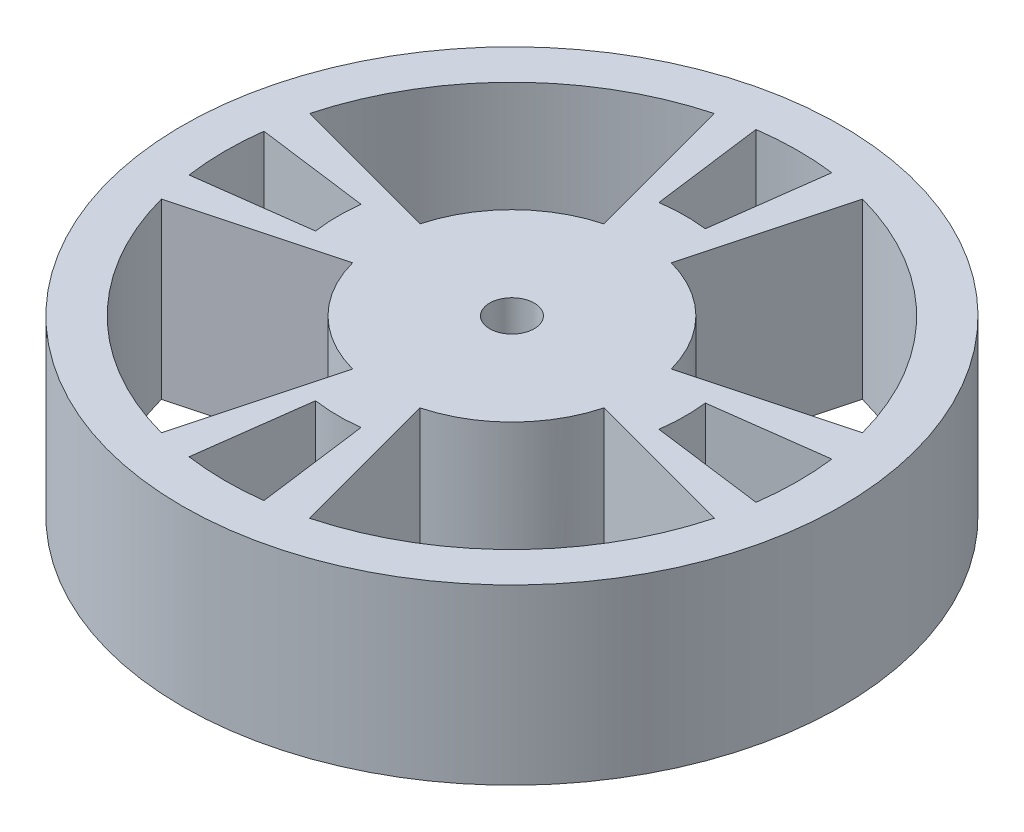
SolidWorks part; units mm, degrees
ref_plane "Front Plane" through (0, 0, 0) normal (0, 0, 1) x (1, 0, 0)
ref_plane "Top Plane" through (0, 0, 0) normal (0, 1, 0) x (1, 0, 0)
ref_plane "Right Plane" through (0, 0, 0) normal (1, 0, 0) x (0, 0, -1)
sketch "Sketch1" plane through (0, 0, 0) normal (0, 1, 0) x (1, 0, 0)
  circle A0 centre (0, 0) radius 9.525
  dimension "D1" = 19.05
extrude "Boss-Extrude1" add sketch "Sketch1" along normal blind 2.54
sketch "Sketch3" plane through (0, 2.54, 0) normal (0, 1, 0) x (1, 0, 0)
  line L0 (0, 0) -> (24.13, 0) construction
  line L1 (0, 0) -> (0, 24.13) construction
  line L2 (0, 0) -> (23.3078, 6.2453) construction
  line L3 (-2.4653, 9.2004) -> (-5.4236, 20.241)
  line L4 (9.2004, 2.4653) -> (20.241, 5.4236)
  line L5 (-9.2004, 2.4653) -> (-20.241, 5.4236)
  line L6 (0, 0) -> (17.0625, 17.0625) construction
  line L8 (2.4653, 9.2004) -> (5.4236, 20.241)
  line L9 (9.2004, -2.4653) -> (20.241, -5.4236)
  line L10 (2.4653, -9.2004) -> (5.4236, -20.241)
  line L11 (-9.2004, -2.4653) -> (-20.241, -5.4236)
  line L12 (-2.4653, -9.2004) -> (-5.4236, -20.241)
  circle A0 centre (0, 0) radius 24.13
  circle A2 centre (0, 0) radius 20.955 construction
  circle A3 centre (0, 0) radius 9.525 construction
  arc A4 (-9.2004, 2.4653) -> (-2.4653, 9.2004) centre (0, 0) cw
  arc A5 (9.2004, 2.4653) -> (2.4653, 9.2004) centre (0, 0) ccw
  arc A8 (20.241, 5.4236) -> (5.4236, 20.241) centre (0, 0) ccw
  arc A9 (-20.241, 5.4236) -> (-5.4236, 20.241) centre (0, 0) cw
  arc A10 (9.2004, -2.4653) -> (2.4653, -9.2004) centre (0, 0) cw
  arc A11 (20.241, -5.4236) -> (5.4236, -20.241) centre (0, 0) cw
  arc A12 (-20.241, -5.4236) -> (-5.4236, -20.241) centre (0, 0) ccw
  arc A13 (-9.2004, -2.4653) -> (-2.4653, -9.2004) centre (0, 0) ccw
  dimension "D1" = 48.26
  dimension "D2" = 15
  dimension "D4" = 3.175
  dimension "D3" = 45
extrude "Boss-Extrude2" add sketch "Sketch3" along normal blind 12.7
sketch "Sketch4" plane through (0, 15.24, 0) normal (0, 1, 0) x (1, 0, 0)
  line L0 (0, 0) -> (24.13, 0) construction
  line L1 (0, 0) -> (0, 24.13) construction
  line L2 (12.6046, 1.5541) -> (20.7891, 2.6316)
  line L5 (12.5705, -1.8088) -> (20.7553, -2.8863)
  line L6 (-12.6046, 1.5541) -> (-20.7891, 2.6316)
  line L7 (-12.5705, -1.8088) -> (-20.7553, -2.8863)
  line L8 (0, 0) -> (17.0625, 17.0625) construction
  line L9 (1.5541, 12.6046) -> (2.6316, 20.7891)
  line L10 (-1.8088, 12.5705) -> (-2.8863, 20.7553)
  line L11 (-1.8088, -12.5705) -> (-2.8863, -20.7553)
  line L12 (1.5541, -12.6046) -> (2.6316, -20.7891)
  circle A2 centre (0, 0) radius 12.7 construction
  arc A3 (-2.4653, 9.2004) -> (-9.2004, 2.4653) centre (0, 0) ccw construction
  circle A4 centre (0, 0) radius 20.955 construction
  arc A5 (12.5705, -1.8088) -> (12.6046, 1.5541) centre (0, 0) ccw
  arc A6 (-5.4236, 20.241) -> (-20.241, 5.4236) centre (0, 0) ccw construction
  circle A7 centre (0, 0) radius 24.13 construction
  arc A8 (20.7553, -2.8863) -> (20.7891, 2.6316) centre (0, 0) ccw
  arc A9 (-12.5705, -1.8088) -> (-12.6046, 1.5541) centre (0, 0) cw
  arc A10 (-20.7553, -2.8863) -> (-20.7891, 2.6316) centre (0, 0) cw
  arc A11 (-1.8088, 12.5705) -> (1.5541, 12.6046) centre (0, 0) cw
  arc A12 (-2.8863, 20.7553) -> (2.6316, 20.7891) centre (0, 0) cw
  arc A13 (-2.8863, -20.7553) -> (2.6316, -20.7891) centre (0, 0) ccw
  arc A14 (-1.8088, -12.5705) -> (1.5541, -12.6046) centre (0, 0) ccw
  dimension "D1" = 3.175
  dimension "D2" = 0
  dimension "D3" = 7.5
  dimension "D4" = 7.5
  dimension "D5" = 45
extrude "Cut-Extrude2" cut sketch "Sketch4" against normal through all
sketch "Sketch2" plane through (0, 0, 0) normal (0, 1, 0) x (1, 0, 0)
  line L1 (-4.5529, 1.8859) -> (-1.8859, 4.5529)
  line L2 (-2.667, 2.667) -> (2.667, -2.667) construction
  line L3 (0, 2.667) -> (-1.8859, 4.5529)
  line L4 (1.8859, 4.5529) -> (4.5529, 1.8859)
  line L5 (0, 2.667) -> (1.8859, 4.5529)
  line L6 (0, -2.667) -> (1.8859, -4.5529)
  line L7 (-4.5529, -1.8859) -> (-1.8859, -4.5529)
  line L8 (-2.667, 0) -> (-4.5529, 1.8859)
  line L9 (1.8859, -4.5529) -> (4.5529, -1.8859)
  line L10 (-2.667, -2.667) -> (2.667, -2.667) construction
  line L11 (-2.667, 0) -> (-4.5529, -1.8859)
  line L12 (2.667, 0) -> (4.5529, 1.8859)
  line L13 (-2.667, 2.667) -> (2.667, 2.667) construction
  line L14 (2.667, 0) -> (4.5529, -1.8859)
  line L15 (2.667, -2.667) -> (2.667, 2.667) construction
  line L16 (-2.667, -2.667) -> (-2.667, 2.667) construction
  line L17 (0, -2.667) -> (-1.8859, -4.5529)
  line L18 (-2.667, -2.667) -> (2.667, 2.667) construction
  point P23 (-2.667, 0)
  dimension "D1" = 3.7717
  dimension "D2" = 2.667
  dimension "D3" = 2.667
  dimension "D4" = 3.7717
  dimension "D5" = 2.667
  dimension "D6" = 2.667
  dimension "D7" = 3.7717
  dimension "D8" = 2.667
  dimension "D9" = 2.667
  dimension "D10" = 3.7717
  dimension "D11" = 2.667
  dimension "D12" = 2.667
  dimension "D13" = 5.334
  dimension "D14" = 5.334
  dimension "D15" = 3.7717
extrude "Cut-Extrude3" cut sketch "Sketch2" along normal blind 8.4667
sketch "Sketch5" plane through (0, 15.24, 0) normal (0, 1, 0) x (1, 0, 0)
  circle A0 centre (0, 0) radius 1.632
  dimension "D1" = 3.2639
extrude "Cut-Extrude4" cut sketch "Sketch5" against normal through all
